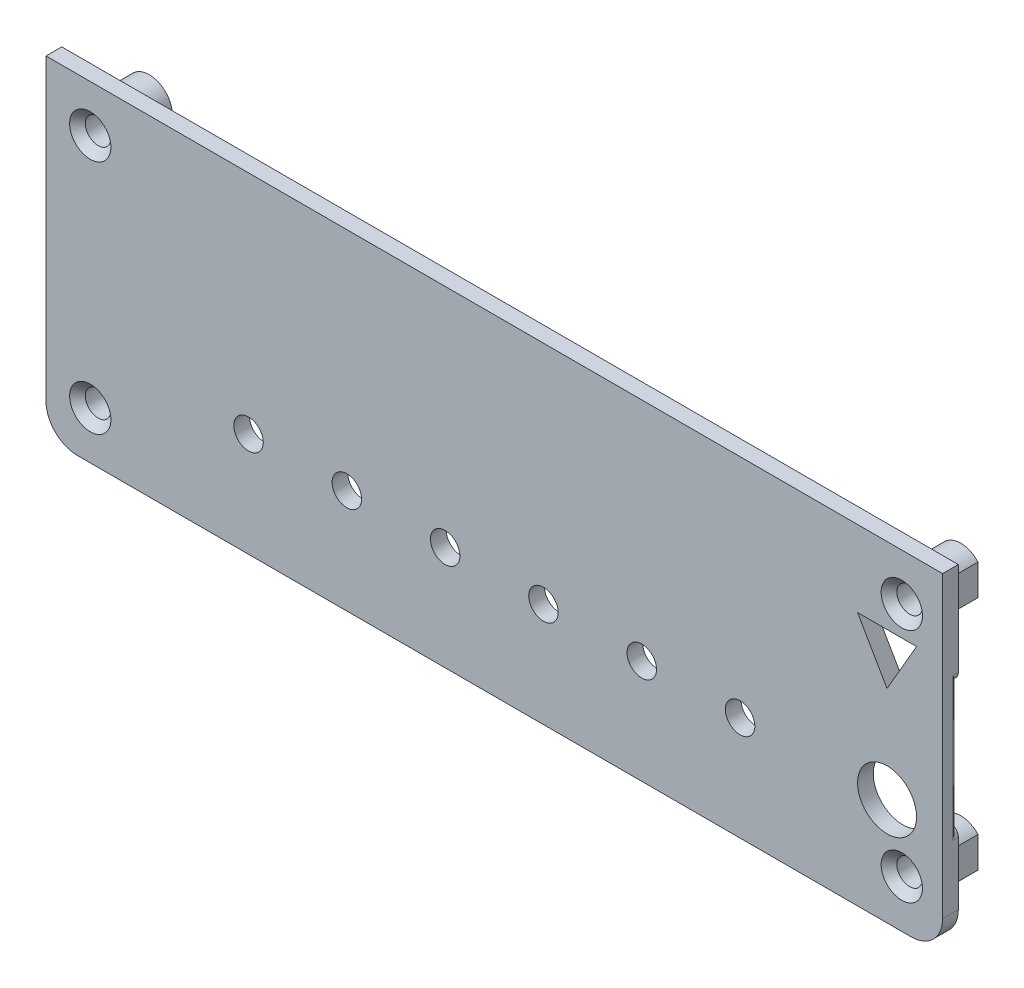
SolidWorks part; units mm, degrees
ref_plane "Спереди" through (0, 0, 0) normal (0, 0, 1) x (1, 0, 0)
ref_plane "Сверху" through (0, 0, 0) normal (0, 1, 0) x (1, 0, 0)
ref_plane "Справа" through (0, 0, 0) normal (1, 0, 0) x (0, 0, -1)
other "Configuration Table"
sketch "Эскиз1" plane through (0, 0, 0) normal (0, 0, 1) x (1, 0, 0)
  line L0 (-43.8, 13.4) -> (-43.8, -13.4)
  line L1 (42.2, 15) -> (-42.2, 15)
  line L2 (-42.2, -15) -> (42.2, -15)
  line L3 (43.8, -13.4) -> (43.8, 13.4)
  line L4 (38.0465, 9.4462) -> (38.0465, 6.6462)
  line L5 (45.6, 16.8) -> (42.6, 16.8)
  line L6 (42.6, 16.8) -> (39.6, 16.8)
  line L7 (39.6, 16.8) -> (-39.6, 16.8)
  line L8 (-39.6, 16.8) -> (-42.6, 16.8)
  line L9 (-42.6, 16.8) -> (-45.6, 16.8)
  line L10 (-45.6, 16.8) -> (-45.6, -13.6)
  line L11 (-42.4, -16.8) -> (42.4, -16.8)
  line L12 (45.6, -13.6) -> (45.6, -7.2038)
  line L13 (44.8, -6.4038) -> (44.8, 6.4962)
  line L14 (45.6, 7.2962) -> (45.6, 16.8)
  line L15 (41.8465, 9.4462) -> (38.0465, 9.4462)
  line L16 (41.8465, 6.6462) -> (41.8465, 9.4462)
  line L17 (38.0465, 6.6462) -> (41.8465, 6.6462)
  line L18 (38.0465, -6.5538) -> (38.0465, -9.3538)
  line L19 (41.8465, -6.5538) -> (38.0465, -6.5538)
  line L20 (41.8465, -9.3538) -> (41.8465, -6.5538)
  line L21 (38.0465, -9.3538) -> (41.8465, -9.3538)
  circle A0 centre (-41.1, 12.0462) radius 1
  circle A1 centre (-41.1, -11.9538) radius 1
  arc A2 (-45.6, -13.6) -> (-42.4, -16.8) centre (-42.4, -13.6) ccw
  arc A3 (42.4, -16.8) -> (45.6, -13.6) centre (42.4, -13.6) ccw
  arc A4 (45.6, -7.2038) -> (44.8, -6.4038) centre (44.8, -7.2038) ccw
  arc A5 (44.8, 6.4962) -> (45.6, 7.2962) centre (44.8, 7.2962) ccw
  arc A6 (-42.2, 15) -> (-43.8, 13.4) centre (-42.2, 13.4) ccw
  arc A7 (-43.8, -13.4) -> (-42.2, -15) centre (-42.2, -13.4) ccw
  arc A8 (43.8, 13.4) -> (42.2, 15) centre (42.2, 13.4) ccw
  arc A9 (42.2, -15) -> (43.8, -13.4) centre (42.2, -13.4) ccw
  circle A10 centre (39.9465, 8.0462) radius 0.8
  circle A11 centre (41.4465, 12.0462) radius 1
  circle A12 centre (39.9465, -7.9538) radius 0.8
  circle A13 centre (41.4465, -11.9538) radius 1
sketch "Эскиз2" plane through (0, 0, 0) normal (0, 0, 1) x (1, 0, 0)
  line L0 (45.6, 16.8) -> (42.6, 16.8) construction
  line L1 (39.6, 16.8) -> (-39.6, 16.8) construction
  line L2 (-39.6, 16.8) -> (-42.6, 16.8) construction
  line L3 (-42.6, 16.8) -> (-45.6, 16.8) construction
  line L4 (-45.6, 16.8) -> (-45.6, -13.6) construction
  line L5 (-42.4, -16.8) -> (42.4, -16.8) construction
  line L6 (45.6, -13.6) -> (45.6, -7.2038) construction
  line L7 (45.6, 7.2962) -> (45.6, 16.8) construction
  line L8 (42.6, 16.8) -> (39.6, 16.8) construction
  line L9 (45.6, -13.6) -> (45.6, -7.2038)
  line L10 (-42.4, -16.8) -> (42.4, -16.8)
  line L11 (-45.6, 16.8) -> (-45.6, -13.6)
  line L12 (-42.6, 16.8) -> (-45.6, 16.8)
  line L13 (-39.6, 16.8) -> (-42.6, 16.8)
  line L14 (39.6, 16.8) -> (-39.6, 16.8)
  line L15 (45.6, 7.2962) -> (45.6, 16.8)
  line L16 (45.6, 16.8) -> (42.6, 16.8)
  line L17 (42.6, 16.8) -> (39.6, 16.8)
  line L18 (45.6, 7.2962) -> (45.6, -7.2038)
  arc A0 (-45.6, -13.6) -> (-42.4, -16.8) centre (-42.4, -13.6) ccw construction
  arc A1 (42.4, -16.8) -> (45.6, -13.6) centre (42.4, -13.6) ccw construction
  arc A2 (42.4, -16.8) -> (45.6, -13.6) centre (42.4, -13.6) ccw
  arc A3 (-45.6, -13.6) -> (-42.4, -16.8) centre (-42.4, -13.6) ccw
extrude "Бобышка-Вытянуть1" add sketch "Эскиз2" along normal blind 1.6
sketch "Эскиз3" plane through (0, 0, 1.6) normal (0, 0, 1) x (1, 0, 0)
  line L0 (-43.8, 13.4) -> (-43.8, -13.4) construction
  line L1 (42.2, 15) -> (-42.2, 15) construction
  line L2 (-43.8, 13.4) -> (-43.8, -13.4)
  line L3 (42.2, 15) -> (-42.2, 15)
  line L4 (43.8, -13.4) -> (43.8, 13.4) construction
  line L5 (-42.2, -15) -> (42.2, -15) construction
  line L6 (43.8, -13.4) -> (43.8, 13.4)
  line L7 (-42.2, -15) -> (42.2, -15)
  arc A0 (-42.2, 15) -> (-43.8, 13.4) centre (-42.2, 13.4) ccw construction
  arc A1 (-42.2, 15) -> (-43.8, 13.4) centre (-42.2, 13.4) ccw
  arc A2 (42.2, -15) -> (43.8, -13.4) centre (42.2, -13.4) ccw construction
  arc A3 (43.8, 13.4) -> (42.2, 15) centre (42.2, 13.4) ccw construction
  arc A4 (-43.8, -13.4) -> (-42.2, -15) centre (-42.2, -13.4) ccw construction
  arc A5 (42.2, -15) -> (43.8, -13.4) centre (42.2, -13.4) ccw
  arc A6 (43.8, 13.4) -> (42.2, 15) centre (42.2, 13.4) ccw
  arc A7 (-43.8, -13.4) -> (-42.2, -15) centre (-42.2, -13.4) ccw
extrude "Вытянуть-Тонкостенный1" add sketch "Эскиз3" against normal blind 2.8 thin
sketch "Эскиз4" plane through (0, 0, -1.2) normal (0, 0, -1) x (-1, 0, 0)
  line L4 (43.8, -13.4) -> (43.8, 13.4)
  line L5 (-42.2, -15) -> (42.2, -15)
  line L6 (-43.8, 13.4) -> (-43.8, -13.4)
  line L7 (42.2, 15) -> (-42.2, 15)
  line L8 (43.8, -13.4) -> (43.8, 13.4)
  line L9 (-42.2, -15) -> (42.2, -15)
  line L10 (-43.8, 13.4) -> (-43.8, -13.4)
  line L11 (42.2, 15) -> (-42.2, 15)
  arc A4 (43.8, 13.4) -> (42.2, 15) centre (42.2, 13.4) ccw
  arc A5 (42.2, -15) -> (43.8, -13.4) centre (42.2, -13.4) ccw
  arc A6 (-43.8, -13.4) -> (-42.2, -15) centre (-42.2, -13.4) ccw
  arc A7 (-42.2, 15) -> (-43.8, 13.4) centre (-42.2, 13.4) ccw
  arc A8 (43.8, 13.4) -> (42.2, 15) centre (42.2, 13.4) ccw
  arc A9 (42.2, -15) -> (43.8, -13.4) centre (42.2, -13.4) ccw
  arc A10 (-43.8, -13.4) -> (-42.2, -15) centre (-42.2, -13.4) ccw
  arc A11 (-42.2, 15) -> (-43.8, 13.4) centre (-42.2, 13.4) ccw
  dimension "D1" = 0
extrude "Вырез-Вытянуть-Тонкостенный1" cut sketch "Эскиз4" against normal blind 1.2 thin thin type one direction reverse wall 0.6
sketch "Эскиз8" plane through (0, 0, 0) normal (0, 0, -1) x (-1, 0, 0)
  circle A0 centre (-41.4465, 12.0462) radius 2.3535
  circle A1 centre (-41.4465, -11.9538) radius 2.3535
  circle A2 centre (41.1, 12.0462) radius 2.3535
  circle A3 centre (41.1, -11.9538) radius 2.3535
  dimension "D1" = 4.7069
extrude "Бобышка-Вытянуть2" add sketch "Эскиз8" along normal blind 4.4
sketch "Эскиз9" plane through (0, 0, 0) normal (0, 0, -1) x (-1, 0, 0)
  line L0 (-44.8, -6.4038) -> (-44.8, 6.4962) construction
  line L1 (-44.8, -6.4038) -> (-44.8, 6.4962)
  line L2 (-45.6, 7.2962) -> (-45.6, -7.2038)
  arc A0 (-45.6, 7.2962) -> (-44.8, 6.4962) centre (-44.8, 7.2962) ccw construction
  arc A1 (-44.8, -6.4038) -> (-45.6, -7.2038) centre (-44.8, -7.2038) ccw construction
  arc A2 (-45.6, 7.2962) -> (-44.8, 6.4962) centre (-44.8, 7.2962) ccw
  arc A3 (-44.8, -6.4038) -> (-45.6, -7.2038) centre (-44.8, -7.2038) ccw
extrude "Вырез-Вытянуть2" cut sketch "Эскиз9" against normal blind 0.2
fillet "Скругление2" radius 0.4 1 edges at (45.6, 0.0462, 0.2)
sketch "Эскиз10" plane through (0, 0, 0) normal (0, 0, -1) x (-1, 0, 0)
  line L1 (-43.2, 14.1046) -> (-45.6, 14.1046)
  line L2 (-43.2, 14.1046) -> (-43.2, -13.6)
  line L3 (-43.2, -13.6) -> (-45.6, -13.6)
  line L4 (-45.6, 14.1046) -> (-45.6, -13.6)
  line L5 (43.2, 14.6794) -> (45.6, 14.6794)
  line L6 (43.2, 14.6794) -> (43.2, -13.6)
  line L7 (43.2, -13.6) -> (45.6, -13.6)
  line L8 (45.6, 14.6794) -> (45.6, -13.6)
extrude "Вырез-Вытянуть3" cut sketch "Эскиз10" along normal blind 12
sketch "Эскиз11" plane through (0, 0, -4.4) normal (0, 0, -1) x (-1, 0, 0)
  circle A0 centre (-41.4465, 12.0462) radius 1.3
  circle A1 centre (-41.4465, -11.9538) radius 1.3
  circle A2 centre (41.1, -11.9538) radius 1.3
  circle A3 centre (41.1, 12.0462) radius 1.3
  dimension "D1" = 2.6
extrude "Вырез-Вытянуть4" cut sketch "Эскиз11" against normal blind 12
chamfer "Фаска1" distance 0.8 angle 45 4 edges at (42.7465, 12.0462, 1.6) (-39.8, 12.0462, 1.6) (-39.8, -11.9538, 1.6) (42.7465, -11.9538, 1.6)
sketch "Эскиз12" plane through (0, 0, 0) normal (0, 0, -1) x (-1, 0, 0)
  line L0 (-42, -9.6664) -> (-42, 9.7587) construction
  line L1 (39.1036, -13.2) -> (-39.4501, -13.2) construction
  line L2 (-35, -6.2) -> (-25, -6.2) construction
  circle A0 centre (-35, -6.2) radius 1.5
  circle A1 centre (-25, -6.2) radius 1.5
  circle A2 centre (-15, -6.2) radius 1.5
  circle A3 centre (-5, -6.2) radius 1.5
  circle A4 centre (5, -6.2) radius 1.5
  circle A5 centre (15, -6.2) radius 1.5
  circle A6 centre (25, -6.2) radius 1.5
  circle A7 centre (35, -6.2) radius 1.5
  dimension "D1" = 3
  dimension "D2" = 7
  dimension "D3" = 7
  dimension "D5" = 10
  dimension "D4" = 8
extrude "Вырез-Вытянуть5" cut sketch "Эскиз12" against normal blind 12
sketch "Эскиз13" plane through (0, 0, 0) normal (0, 0, -1) x (-1, 0, 0)
  line L0 (-42.9465, 9.0462) -> (-36.9465, 9.0462)
  line L1 (-36.9465, 9.0462) -> (-39.9465, 3.85)
  line L2 (-39.9465, 3.85) -> (-42.9465, 9.0462)
  line L3 (-39.9465, 8.0462) -> (-39.9465, -7.9538) construction
  circle A1 centre (-39.9465, -5.9538) radius 3
  circle A2 centre (-39.9465, -7.9538) radius 0.8 construction
  dimension "D1" = 6
  dimension "D6" = 2
  dimension "D2" = 6
  dimension "D3" = 6
  dimension "D4" = 6
  dimension "D5" = 1
extrude "Вырез-Вытянуть6" cut sketch "Эскиз13" against normal blind 12
sketch "Эскиз14" plane through (0, 0, -1.2) normal (0, 0, -1) x (-1, 0, 0)
  line L2 (-42, -9.6664) -> (-42, 9.7587)
  line L3 (-43.2, 10.4764) -> (-43.2, -10.3841)
  line L4 (-42, -9.6664) -> (-42, 9.7587)
  line L5 (-43.2, 10.4764) -> (-43.2, -10.3841)
  arc A2 (-42, -9.6664) -> (-43.2, -10.3841) centre (-41.4465, -11.9538) ccw
  arc A3 (-43.2, 10.4764) -> (-42, 9.7587) centre (-41.4465, 12.0462) ccw
  arc A4 (-42, -9.6664) -> (-43.2, -10.3841) centre (-41.4465, -11.9538) ccw
  arc A5 (-43.2, 10.4764) -> (-42, 9.7587) centre (-41.4465, 12.0462) ccw
  dimension "D1" = 0
extrude "Вырез-Вытянуть7" cut sketch "Эскиз14" against normal blind 1.2
sketch "Эскиз15" plane through (0, 0, 0) normal (0, 0, -1) x (-1, 0, 0)
  circle A0 centre (35, -6.2) radius 1.5 construction
  circle A1 centre (-35, -6.2) radius 1.5 construction
  circle A2 centre (35, -6.2) radius 1.5
  circle A3 centre (-35, -6.2) radius 1.5
extrude "Бобышка-Вытянуть4" add sketch "Эскиз15" against normal blind 1.6
